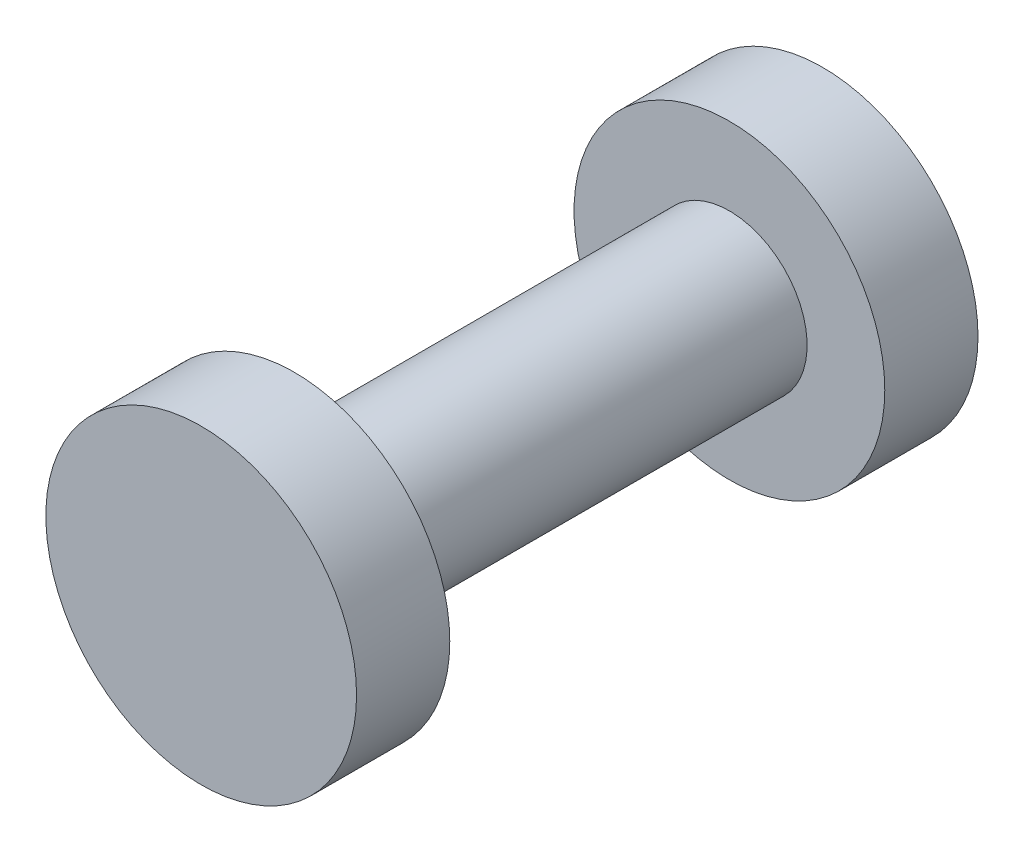
SolidWorks part; units mm, degrees
ref_plane "Front Plane" through (0, 0, 0) normal (0, 0, 1) x (1, 0, 0)
ref_plane "Top Plane" through (0, 0, 0) normal (0, 1, 0) x (1, 0, 0)
ref_plane "Right Plane" through (0, 0, 0) normal (1, 0, 0) x (0, 0, -1)
sketch "Sketch1" plane through (0, 0, 0) normal (0, 0, 1) x (1, 0, 0)
  circle A0 centre (0, 0) radius 1.5
  dimension "D1" = 3
extrude "Boss-Extrude1" add sketch "Sketch1" along normal mid plane 12
sketch "Sketch2" plane through (0, 0, 6) normal (0, 0, 1) x (1, 0, 0)
  circle A0 centre (0, 0) radius 3
  dimension "D1" = 6
extrude "Boss-Extrude2" add sketch "Sketch2" against normal blind 1.8
mirror "Mirror1" about plane through (0, 0, 0) normal (0, 0, 1) of "Boss-Extrude2"
